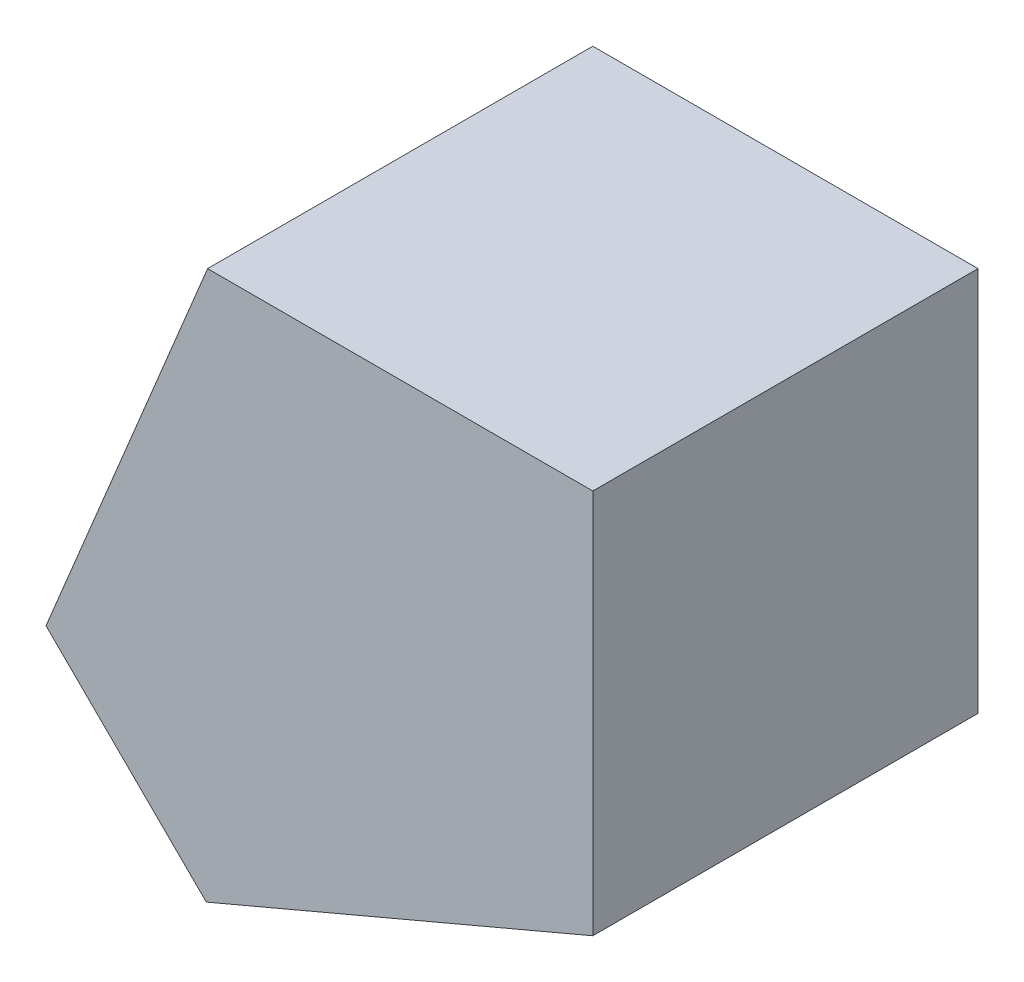
SolidWorks part; units mm, degrees
ref_plane "前视基准面" through (0, 0, 0) normal (0, 0, 1) x (1, 0, 0)
ref_plane "上视基准面" through (0, 0, 0) normal (0, 1, 0) x (1, 0, 0)
ref_plane "右视基准面" through (0, 0, 0) normal (1, 0, 0) x (0, 0, -1)
sketch "草图1" plane through (0, 0, 0) normal (0, 0, 1) x (1, 0, 0)
  line L0 (16.6248, 11.2471) -> (16.6248, 16.2471)
  line L1 (16.6248, 16.2471) -> (11.6248, 16.2471)
  line L2 (11.6248, 16.2471) -> (9.5273, 11.1834)
  line L3 (11.608, 9.1176) -> (16.6248, 11.2471)
  line L4 (11.608, 9.1176) -> (9.5273, 11.1834)
  dimension "D1" = 5
  dimension "D2" = 5.45
extrude "凸台-拉伸1" add sketch "草图1" along normal blind 5
